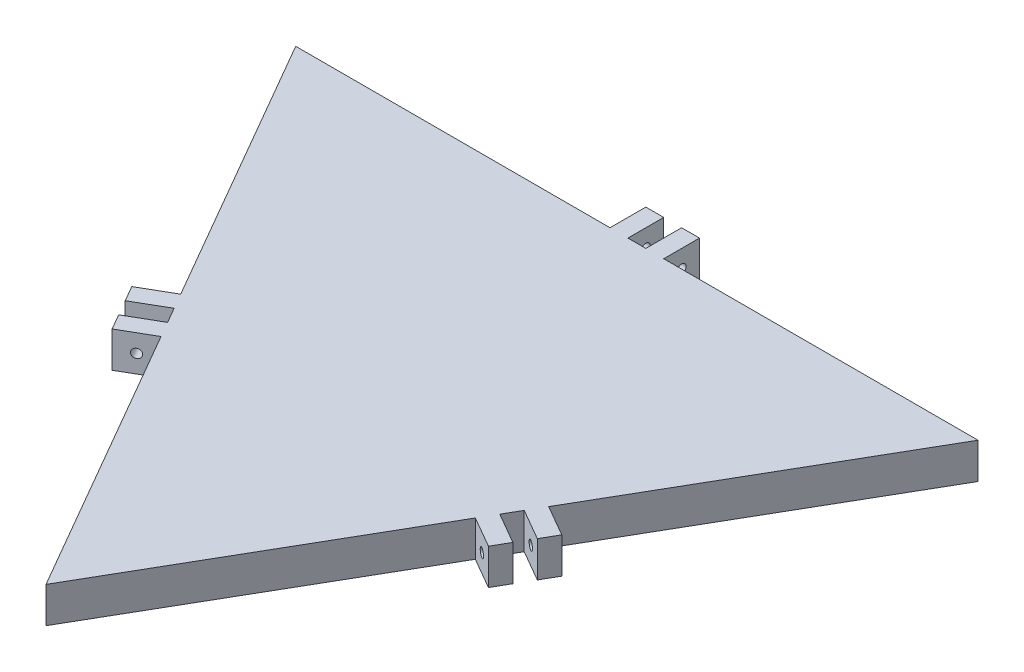
SolidWorks part; units mm, degrees
ref_plane "Front Plane" through (0, 0, 0) normal (0, 0, 1) x (1, 0, 0)
ref_plane "Top Plane" through (0, 0, 0) normal (0, 1, 0) x (1, 0, 0)
ref_plane "Right Plane" through (0, 0, 0) normal (1, 0, 0) x (0, 0, -1)
sketch "Sketch2" plane through (0, 0, 0) normal (0, 1, 0) x (1, 0, 0)
  line L0 (-190.55, 110.0141) -> (190.55, 110.0141)
  line L1 (0, -220.0282) -> (190.55, 110.0141)
  line L2 (0, -220.0282) -> (-190.55, 110.0141)
  circle A0 centre (0, 0) radius 110.0141
  point P23 (0, 0)
  dimension "D4" = 381.1
extrude "Boss-Extrude1" add sketch "Sketch2" along normal blind 20 contours L2 L1 L0 A0 | A0
sketch "Sketch3" plane through (95.275, 0, 55.007) normal (0.866, 0, 0.5) x (0.5, 0, -0.866)
  line L1 (-5, 20) -> (-15, 20)
  line L2 (-5, 20) -> (-5, 0)
  line L3 (-5, 0) -> (-15, 0)
  line L4 (-15, 20) -> (-15, 0)
  line L6 (0, 20) -> (0, 0) construction
  line L7 (5, 20) -> (15, 20)
  line L8 (5, 20) -> (5, 0)
  line L9 (5, 0) -> (15, 0)
  line L10 (15, 20) -> (15, 0)
  line L11 (-190.55, 20) -> (190.55, 20) construction
  line L12 (-190.55, 0) -> (190.55, 0) construction
  point P4 (0, 0)
  point P7 (0, 0)
  point P16 (0, 0)
  point P17 (0, 0)
  dimension "D1" = 10
  dimension "D2" = 5
  dimension "D3" = 5
extrude "Boss-Extrude2" add sketch "Sketch3" along normal blind 20
ref_plane "Plane1" through (0, 0, 0) normal (1, 0, 0) x (0, 0, -1)
ref_plane "Plane2" through (0, 0, 0) normal (0.5, 0, 0.866) x (0.866, 0, -0.5)
sketch "Sketch4" plane through (-7.5, 0, 12.9904) normal (-0.5, 0, 0.866) x (0.866, 0, 0.5)
  line L0 (130.0141, 20) -> (110.0141, 20) construction
  line L1 (130.0141, 20) -> (130.0141, 0) construction
  circle A0 centre (120.0141, 10) radius 2.5
  point P4 (120.0141, 20)
  point P7 (130.0141, 10)
  dimension "D1" = 5
extrude "Cut-Extrude1" cut sketch "Sketch4" against normal up to surface (30 mm away) up to face at (111.4353, 10, 47.0167)
mirror "Mirror1" about plane through (0, 0, 0) normal (0.5, 0, 0.866) of "Cut-Extrude1", "Boss-Extrude2" second plane through (0, 0, 0) second plane normal (1, 0, 0)
equation "\"D3@Sketch3\"=\"D2@Sketch3\""
